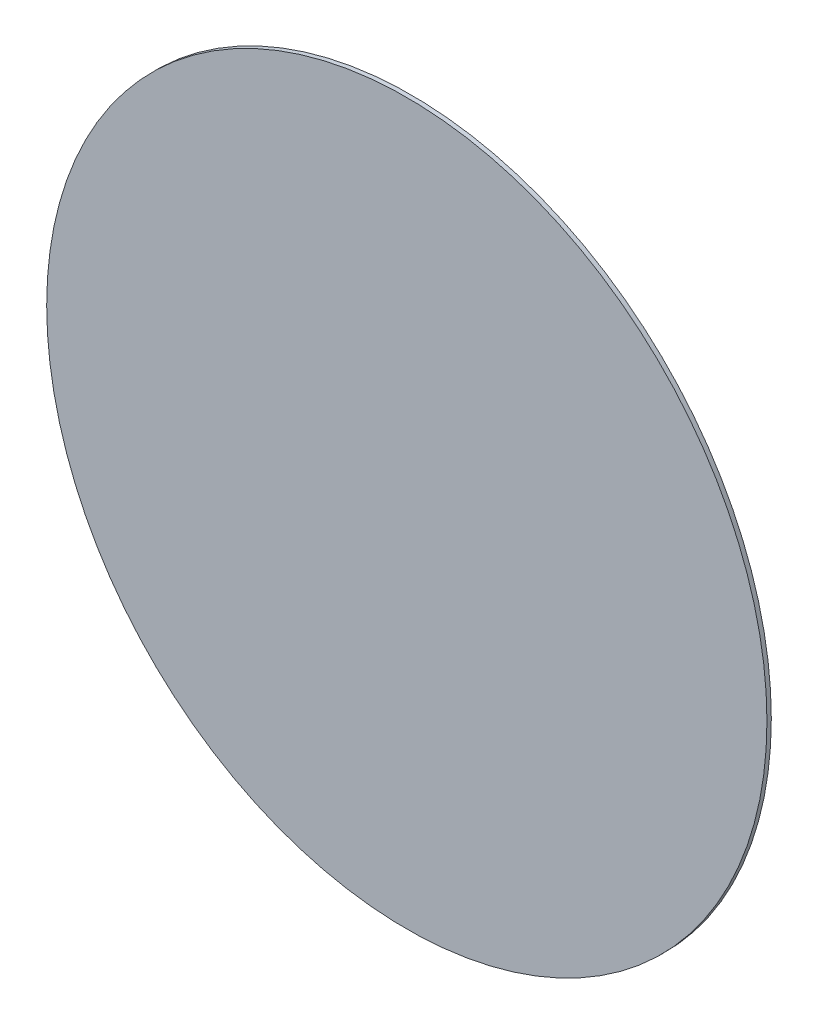
SolidWorks part; units mm, degrees
ref_plane "Front Plane" through (0, 0, 0) normal (0, 0, 1) x (1, 0, 0)
ref_plane "Top Plane" through (0, 0, 0) normal (0, 1, 0) x (1, 0, 0)
ref_plane "Right Plane" through (0, 0, 0) normal (1, 0, 0) x (0, 0, -1)
sketch "Sketch1" plane through (0, 0, 0) normal (0, 0, 1) x (1, 0, 0)
  circle A0 centre (0, 0) radius 16.5
  dimension "D1" = 33
extrude "Boss-Extrude1" add sketch "Sketch1" along normal blind 0.2
